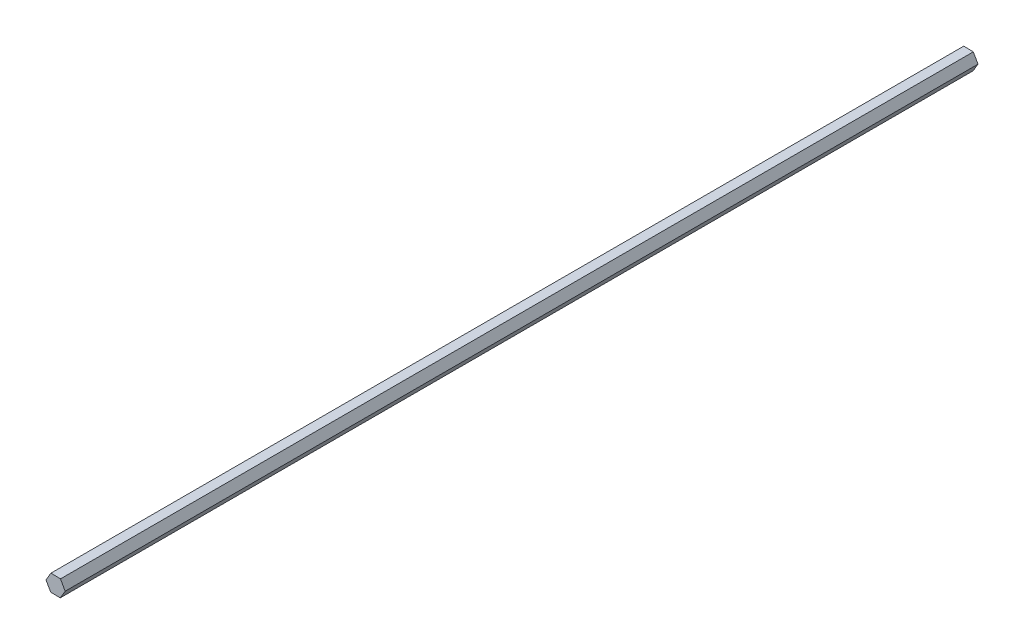
SolidWorks part; units mm, degrees
ref_plane "Front Plane" through (0, 0, 0) normal (0, 0, 1) x (1, 0, 0)
ref_plane "Top Plane" through (0, 0, 0) normal (0, 1, 0) x (1, 0, 0)
ref_plane "Right Plane" through (0, 0, 0) normal (1, 0, 0) x (0, 0, -1)
sketch "Sketch1" plane through (0, 0, 0) normal (0, 0, 1) x (1, 0, 0)
  line L1 (3.5732, -6.4028) -> (7.3316, -0.1069)
  line L2 (7.3316, -0.1069) -> (3.7584, 6.2959)
  line L3 (3.7584, 6.2959) -> (-3.5732, 6.4028)
  line L4 (-3.5732, 6.4028) -> (-7.3316, 0.1069)
  line L5 (-7.3316, 0.1069) -> (-3.7584, -6.2959)
  line L6 (-3.7584, -6.2959) -> (3.5732, -6.4028)
  circle A0 centre (0, 0) radius 6.35 construction
  dimension "D2" = 12.7
extrude "Boss-Extrude1" add sketch "Sketch1" along normal blind 698.5
